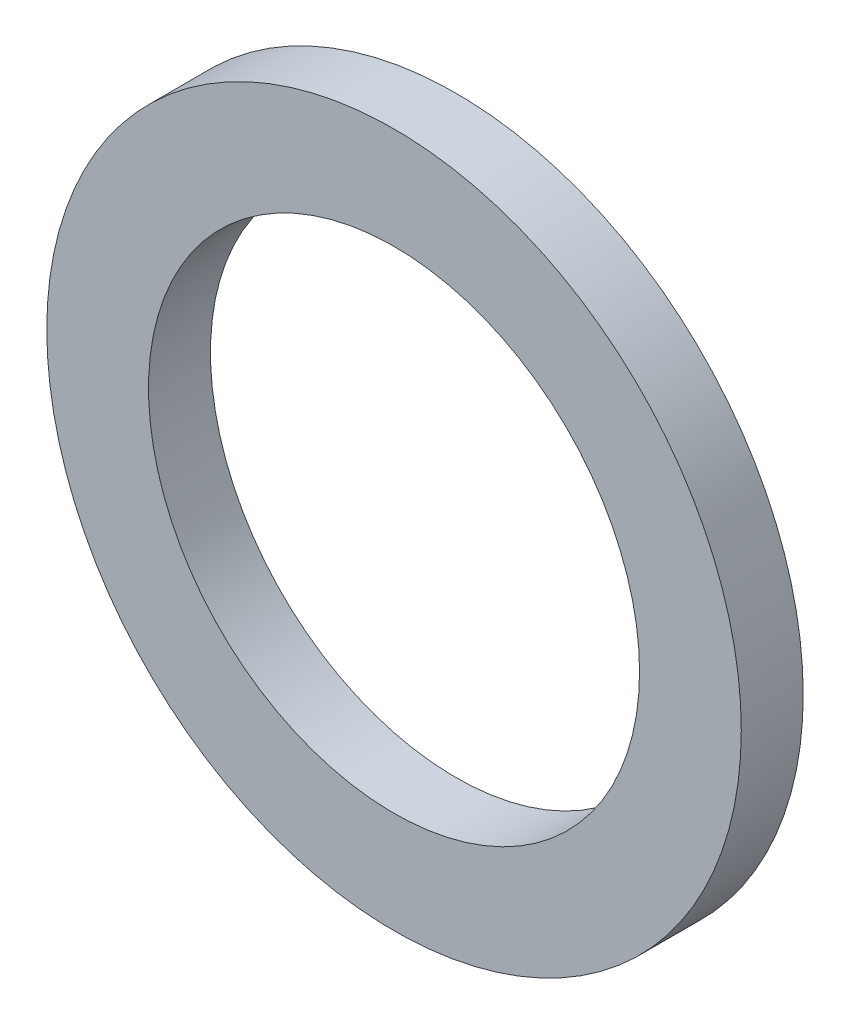
SolidWorks part; units mm, degrees
ref_plane "Front Plane" through (0, 0, 0) normal (0, 0, 1) x (1, 0, 0)
ref_plane "Top Plane" through (0, 0, 0) normal (0, 1, 0) x (1, 0, 0)
ref_plane "Right Plane" through (0, 0, 0) normal (1, 0, 0) x (0, 0, -1)
sketch "Sketch1" plane through (0, 0, 0) normal (0, 0, 1) x (1, 0, 0)
  circle A0 centre (0, 0) radius 5.55
  circle A1 centre (0, 0) radius 7.85
  dimension "D1" = 2.3
  dimension "D2" = 15.7
extrude "Boss-Extrude1" add sketch "Sketch1" along normal blind 1.4
